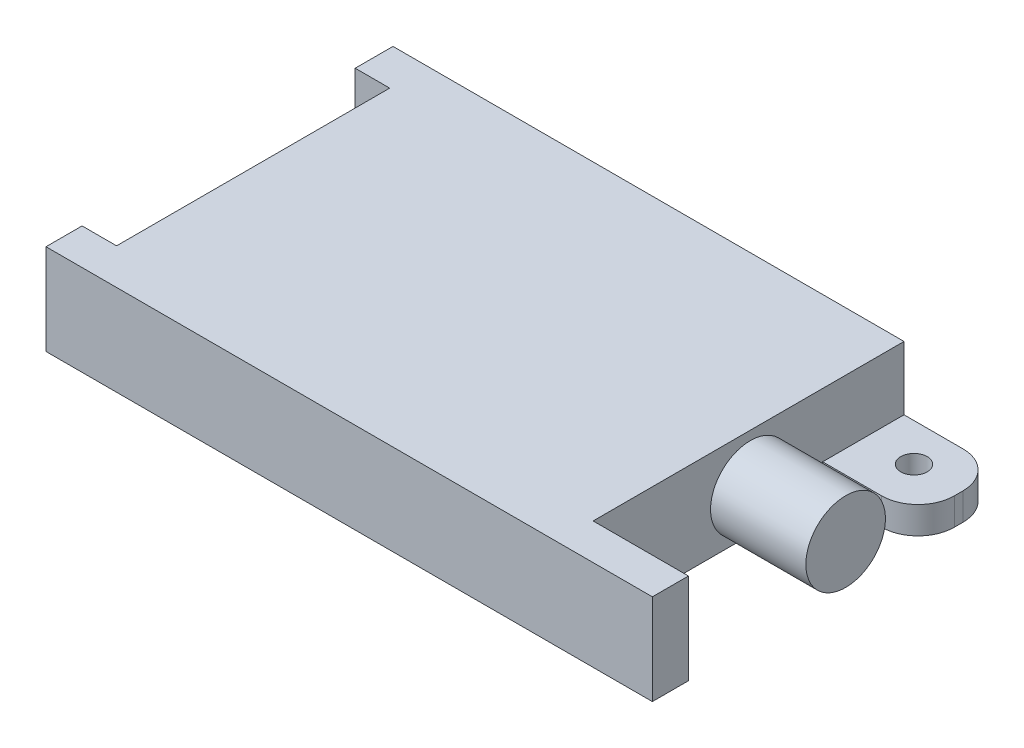
SolidWorks part; units mm, degrees
ref_plane "Front Plane" through (0, 0, 0) normal (0, 0, 1) x (1, 0, 0)
ref_plane "Top Plane" through (0, 0, 0) normal (0, 1, 0) x (1, 0, 0)
ref_plane "Right Plane" through (0, 0, 0) normal (1, 0, 0) x (0, 0, -1)
sketch "Sketch1" plane through (0, 0, 0) normal (0, 1, 0) x (1, 0, 0)
  line L0 (-61.1312, -32.9314) -> (72.4868, -32.9314)
  line L1 (72.4868, -32.9314) -> (72.4868, -24.9824)
  line L2 (72.4868, -24.9824) -> (51.4824, -24.9824)
  line L3 (51.4824, -24.9824) -> (51.4824, 25.6007)
  line L4 (51.4824, 25.6007) -> (72.4868, 25.6007)
  line L5 (72.4868, 25.6007) -> (72.4868, 43.53)
  line L6 (72.4868, 43.53) -> (-61.1312, 43.53)
  line L7 (-61.1312, 43.53) -> (-61.1312, 35.2025)
  line L8 (-61.1312, 35.2025) -> (-53.5292, 35.2025)
  line L9 (-53.5292, 35.2025) -> (-53.5292, -24.9824)
  line L10 (-53.5292, -24.9824) -> (-61.1312, -24.9824)
  line L11 (-61.1312, -24.9824) -> (-61.1312, -32.9314)
extrude "Boss-Extrude1" add sketch "Sketch1" along normal blind 20
fillet "Fillet1" radius 8 2 edges at (72.4868, 10, -43.53) (72.4868, 10, -25.6007)
sketch "Sketch2" plane through (0, 20, 0) normal (0, 1, 0) x (1, 0, 0)
  line L0 (51.4824, -24.9824) -> (51.4824, 25.6007) construction
  line L1 (51.4824, 21.0327) -> (76.8987, 21.0327)
  line L2 (51.4824, 21.0327) -> (51.4824, 47.7321)
  line L3 (51.4824, 47.7321) -> (76.8987, 47.7321)
  line L4 (76.8987, 21.0327) -> (76.8987, 47.7321)
extrude "Cut-Extrude1" cut sketch "Sketch2" against normal blind 14
sketch "Sketch3" plane through (0, 6, 0) normal (0, 1, 0) x (1, 0, 0)
  circle A0 centre (62.0102, 35.1951) radius 2.9202
extrude "Cut-Extrude2" cut sketch "Sketch3" against normal through all
sketch "Sketch4" plane through (51.4824, 0, 0) normal (1, 0, 0) x (0, 0, -1)
  circle A0 centre (9.656, 9.244) radius 8.7681
extrude "Boss-Extrude2" add sketch "Sketch4" along normal up to surface (21.0045 mm away) up to face at (72.4868, 10, 28.9569)
